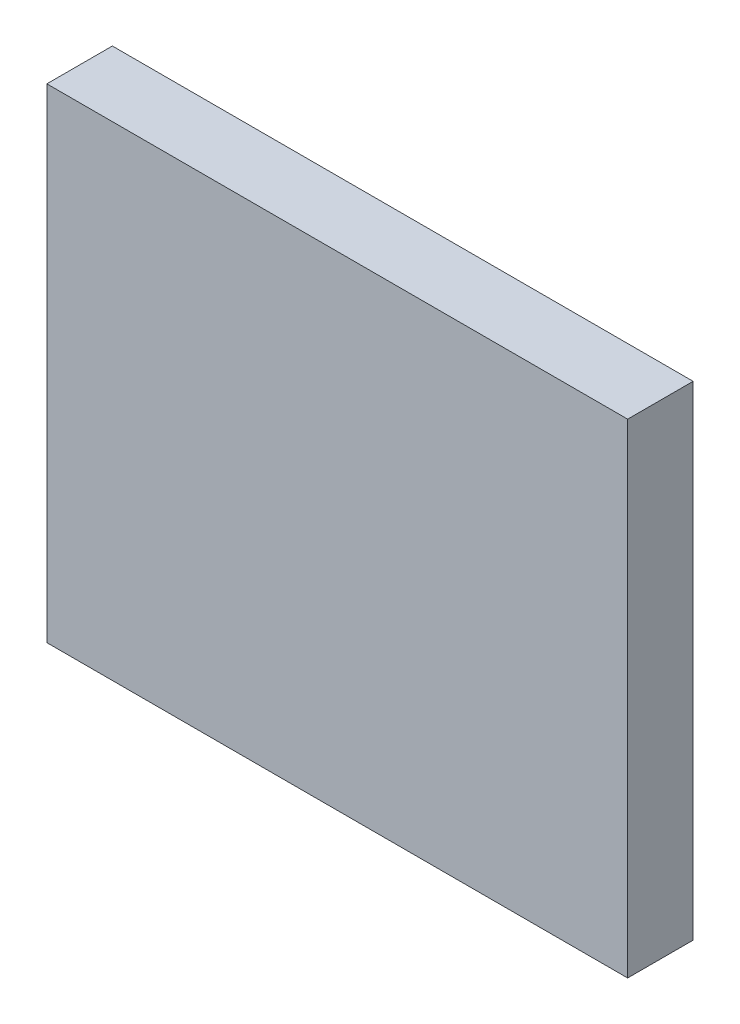
SolidWorks part; units mm, degrees
ref_plane "Front Plane" through (0, 0, 0) normal (0, 0, 1) x (1, 0, 0)
ref_plane "Top Plane" through (0, 0, 0) normal (0, 1, 0) x (1, 0, 0)
ref_plane "Right Plane" through (0, 0, 0) normal (1, 0, 0) x (0, 0, -1)
sketch "Sketch5" plane through (0, 0, 0) normal (0, 0, 1) x (1, 0, 0)
  line L1 (-90, 75) -> (90, 75)
  line L2 (-90, 75) -> (-90, -75)
  line L3 (-90, -75) -> (90, -75)
  line L4 (90, 75) -> (90, -75)
  line L5 (-90, 75) -> (90, -75) construction
  line L6 (-90, -75) -> (90, 75) construction
  point P0 (0, 0)
extrude "Boss-Extrude1" add sketch "Sketch5" along normal blind 20.3
